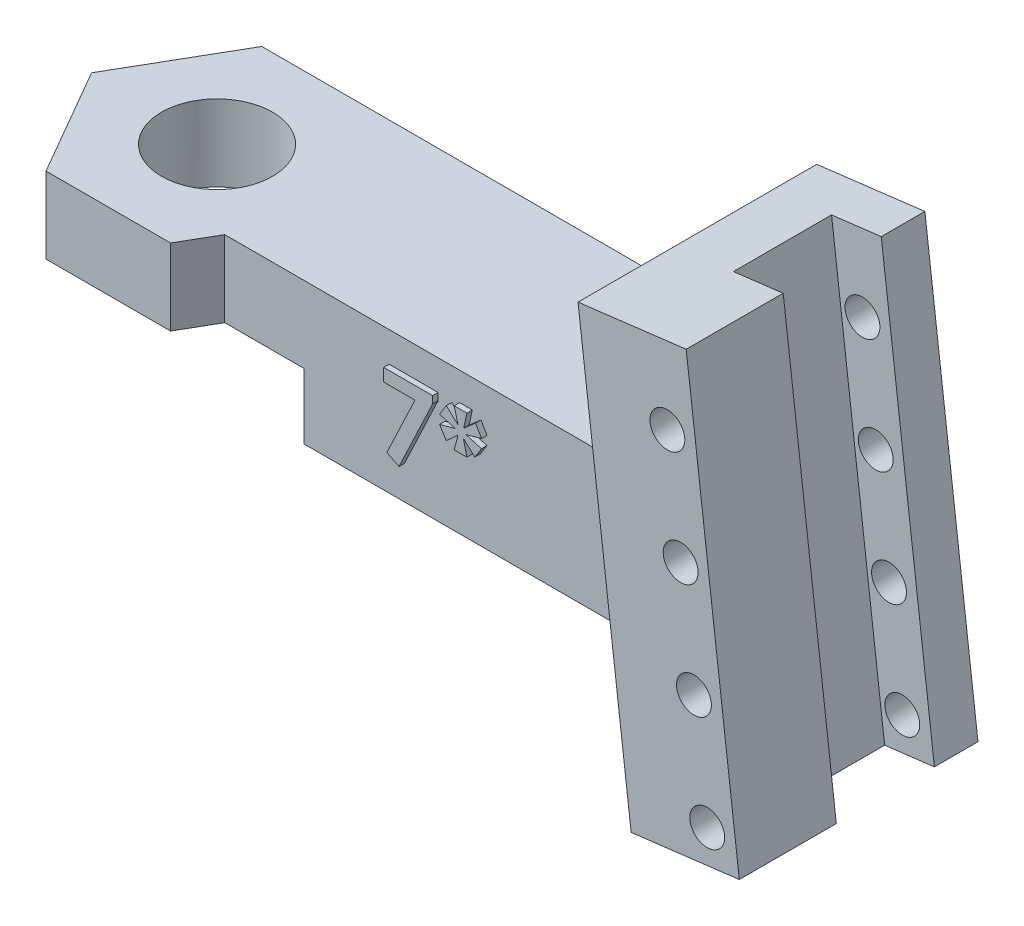
SolidWorks part; units mm, degrees
ref_plane "Front Plane" through (0, 0, 0) normal (0, 0, 1) x (1, 0, 0)
ref_plane "Top Plane" through (0, 0, 0) normal (0, 1, 0) x (1, 0, 0)
ref_plane "Right Plane" through (0, 0, 0) normal (1, 0, 0) x (0, 0, -1)
sketch "Sketch1" plane through (0, 0, 0) normal (0, 1, 0) x (1, 0, 0)
  line L1 (0, 0) -> (25, 0)
  line L2 (0, 0) -> (0, -6.75)
  line L3 (0, -6.75) -> (25, -6.75)
  line L4 (25, 0) -> (25, -6.75)
  dimension "D1" = 6.75
  dimension "D2" = 25
extrude "Boss-Extrude1" add sketch "Sketch1" along normal blind 6.5
ref_plane "Plane1" through (0, 0, 3.375) normal (0, 0, 1) x (1, 0, 0)
sketch "Sketch5" plane through (0, 6.5, 0) normal (0, 1, 0) x (1, 0, 0)
  line L0 (0, 0) -> (0, -6.75) construction
  line L1 (-5.7158, -3.375) -> (-2.8579, -8.325)
  line L2 (-2.8579, -8.325) -> (2.8579, -8.325)
  line L3 (2.8579, -8.325) -> (5.7158, -3.375)
  line L4 (5.7158, -3.375) -> (2.8579, 1.575)
  line L5 (2.8579, 1.575) -> (-2.8579, 1.575)
  line L6 (-2.8579, 1.575) -> (-5.7158, -3.375)
  circle A0 centre (0, -3.375) radius 4.95 construction
  dimension "D1" = 4.95
extrude "Boss-Extrude4" add sketch "Sketch5" against normal up to surface (6.5 mm away) up to face at (12.5, 0, 3.375)
sketch "Sketch3" plane through (0, 0, 3.375) normal (0, 0, 1) x (1, 0, 0)
  line L0 (22.5999, 14.5462) -> (27.5626, 15.1556)
  line L1 (27.5626, 15.1556) -> (30, -4.6953)
  line L2 (30, -4.6953) -> (25.0373, -5.3047)
  line L3 (25.0373, -5.3047) -> (22.5999, 14.5462)
  line L4 (3.7672, 6.5) -> (25, 6.5) construction
  point P6 (27.5186, -5)
  dimension "D1" = 30
  dimension "D2" = 5
  dimension "D3" = 20
  dimension "D4" = 83
  dimension "D6" = 5
extrude "Boss-Extrude3" add sketch "Sketch3" against normal up to surface (4.95 mm away) and the other way blind 6 up to face at (0, 3.25, -1.575)
sketch "Sketch4" plane through (-1.4239, 11.5965, 0) normal (-0.1219, 0.9925, 0) x (0.9925, 0.1219, 0)
  line L0 (29.2042, -9.375) -> (29.2042, 1.575) construction
  line L1 (26.9042, -0.425) -> (29.2042, -0.425)
  line L2 (26.9042, -0.425) -> (26.9042, -4.925)
  line L3 (26.9042, -4.925) -> (29.2042, -4.925)
  line L4 (29.2042, -0.425) -> (29.2042, -4.925)
  line L6 (29.2042, 1.575) -> (24.2042, 1.575) construction
  dimension "D1" = 4.5
  dimension "D2" = 2.3
  dimension "D3" = 2
extrude "Cut-Extrude1" cut sketch "Sketch4" against normal blind 23 contours L2 L3 L4 L1
sketch "Sketch6" plane through (0, 6.5, 0) normal (0, 1, 0) x (1, 0, 0)
  circle A0 centre (0, -3.3356) radius 2.55
  dimension "D1" = 5.1
extrude "Cut-Extrude2" cut sketch "Sketch6" against normal blind 10
sketch "Sketch7" plane through (0, 0, -1.575) normal (0, 0, -1) x (-1, 0, 0)
  line L0 (-2.8579, 0) -> (-24.3859, 0)
  line L1 (-24.3859, 0) -> (-25.0373, -5.3047)
  line L2 (-25.0373, -5.3047) -> (-30, -4.6953)
  line L3 (-30, -4.6953) -> (-27.5626, 15.1556)
  line L4 (-27.5626, 15.1556) -> (-22.5999, 14.5462)
  line L5 (-22.5999, 14.5462) -> (-23.5878, 6.5)
  line L6 (-23.5878, 6.5) -> (-2.8579, 6.5)
  line L7 (-2.8579, 6.5) -> (-2.8579, 0)
  dimension "D1" = 20
extrude "Boss-Extrude5" add sketch "Sketch7" against normal up to surface (1.575 mm away) up to face at (13.877, 3.25, 0)
sketch "Sketch8" plane through (0, 0, 0) normal (0, -1, 0) x (-1, 0, 0)
  line L1 (-4.6765, -11.475) -> (4.6765, -11.475)
  line L2 (4.6765, -11.475) -> (9.3531, -3.375)
  line L3 (9.3531, -3.375) -> (4.6765, 4.725)
  line L4 (4.6765, 4.725) -> (-4.6765, 4.725)
  line L5 (-4.6765, 4.725) -> (-9.3531, -3.375)
  line L6 (-9.3531, -3.375) -> (-4.6765, -11.475)
  circle A0 centre (0, -3.375) radius 8.1 construction
  dimension "D1" = 16.2
extrude "Cut-Extrude3" cut sketch "Sketch8" against normal blind 3
sketch "Sketch9" plane through (0, 0, -1.575) normal (0, 0, -1) x (-1, 0, 0)
  line L0 (-30, -4.6953) -> (-27.5626, 15.1556) construction
  line L1 (-25.0373, -5.3047) -> (-30, -4.6953) construction
  line L2 (-28.5269, -3.3649) -> (-26.6988, 11.5233) construction
  line L3 (-30, -4.6953) -> (-27.5626, 15.1556) construction
  circle A0 centre (-28.5269, -3.3649) radius 0.8
  circle A4 centre (-27.9175, 1.5978) radius 0.8
  circle A5 centre (-27.3082, 6.5605) radius 0.8
  circle A6 centre (-26.6988, 11.5233) radius 0.8
  dimension "D1" = 1.6
  dimension "D2" = 1.3
  dimension "D5" = 5
  dimension "D3" = 1.5
  dimension "D4" = 5
  dimension "D6" = 5
extrude "Cut-Extrude4" cut sketch "Sketch9" against normal up to surface (10.95 mm away) up to face at (26.2999, 4.9255, 9.375)
sketch "Sketch10" plane through (0, 0, 6.75) normal (0, 0, 1) x (1, 0, 0)
  text T0 "<b>7*</b>"
extrude "Boss-Extrude6" add sketch "Sketch10" along normal blind 0.25
